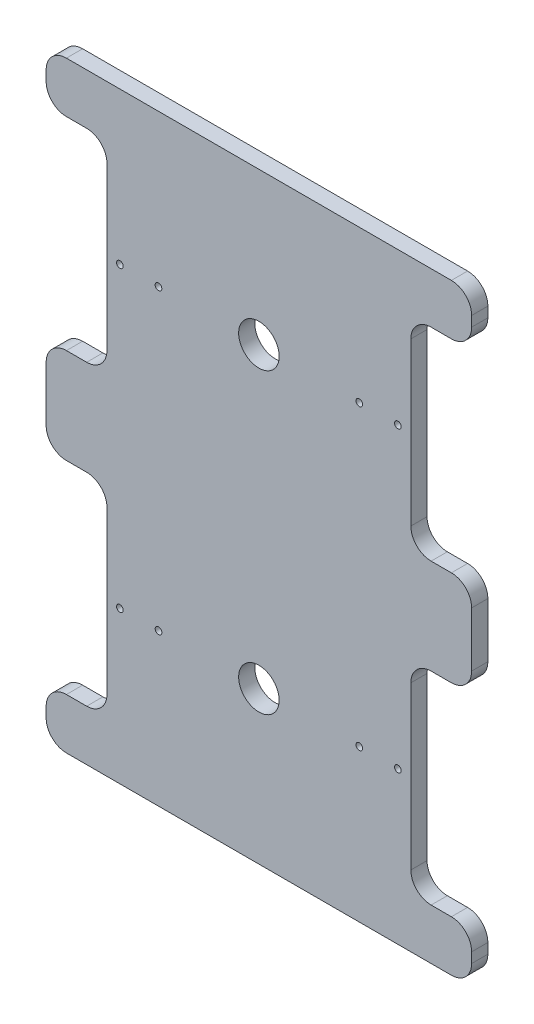
SolidWorks part; units mm, degrees
ref_plane "Přední rovina" through (0, 0, 0) normal (0, 0, 1) x (1, 0, 0)
ref_plane "Horní rovina" through (0, 0, 0) normal (0, 1, 0) x (1, 0, 0)
ref_plane "Pravá rovina" through (0, 0, 0) normal (1, 0, 0) x (0, 0, -1)
sketch "Skica1" plane through (0, 0, 0) normal (0, 0, 1) x (1, 0, 0)
  line L0 (0, 0) -> (210, 0)
  line L1 (210, 0) -> (210, 25)
  line L2 (210, 25) -> (180, 25)
  line L3 (180, 25) -> (180, 125)
  line L4 (180, 125) -> (210, 125)
  line L5 (210, 125) -> (210, 172)
  line L6 (210, 172) -> (180, 172)
  line L7 (180, 172) -> (180, 272)
  line L8 (180, 272) -> (210, 272)
  line L9 (210, 272) -> (210, 297)
  line L10 (210, 297) -> (0, 297)
  line L11 (0, 297) -> (0, 272)
  line L12 (0, 272) -> (30, 272)
  line L13 (30, 272) -> (30, 172)
  line L14 (30, 172) -> (0, 172)
  line L15 (0, 172) -> (0, 125)
  line L16 (0, 125) -> (30, 125)
  line L17 (30, 125) -> (30, 25)
  line L18 (30, 25) -> (0, 25)
  line L19 (0, 25) -> (0, 0)
  dimension "D1" = 210
  dimension "D2" = 297
  dimension "D3" = 100
  dimension "D4" = 100
  dimension "D5" = 25
  dimension "D6" = 25
  dimension "D7" = 30
  dimension "D8" = 30
extrude "Přidat vysunutím2" add sketch "Skica1" along normal blind 8
fillet "Zaoblit1" radius 10 20 edges at (30, 125, 4) (30, 272, 4) (30, 172, 4) (30, 25, 4) (180, 125, 4) (180, 25, 4) (180, 172, 4) (180, 272, 4) (0, 272, 4) (0, 125, 4) (0, 172, 4) (0, 25, 4) (0, 0, 4) (210, 0, 4) (210, 25, 4) (210, 125, 4) (210, 172, 4) (210, 272, 4) (210, 297, 4) (0, 297, 4)
sketch "Skica2" plane through (0, 0, 0) normal (0, 0, -1) x (-1, 0, 0)
  line L2 (-180, 182) -> (-180, 262) construction
  line L3 (-30, 262) -> (-30, 182) construction
  line L4 (-210, 282) -> (-210, 287) construction
  circle A0 centre (-173.6, 222) radius 1.65
  circle A1 centre (-36.4, 222) radius 1.65
  circle A2 centre (-55.45, 222) radius 1.65
  circle A3 centre (-154.55, 222) radius 1.65
  circle A4 centre (-173.6, 75) radius 1.65
  circle A5 centre (-154.55, 75) radius 1.65
  circle A6 centre (-55.45, 75) radius 1.65
  circle A7 centre (-36.4, 75) radius 1.65
  circle A8 centre (-105, 75) radius 10
  circle A9 centre (-105, 222) radius 10
  point P35 (-210, 284.5)
  dimension "D7" = 3.3
  dimension "D9" = 20
  dimension "D10" = 20
  dimension "D1" = 40
  dimension "D2" = 40
  dimension "D3" = 6.4
  dimension "D4" = 19.05
  dimension "D5" = 6.4
  dimension "D6" = 19.05
  dimension "D8" = 105
extrude "Odebrat vysunutím1" cut sketch "Skica2" against normal blind 8
